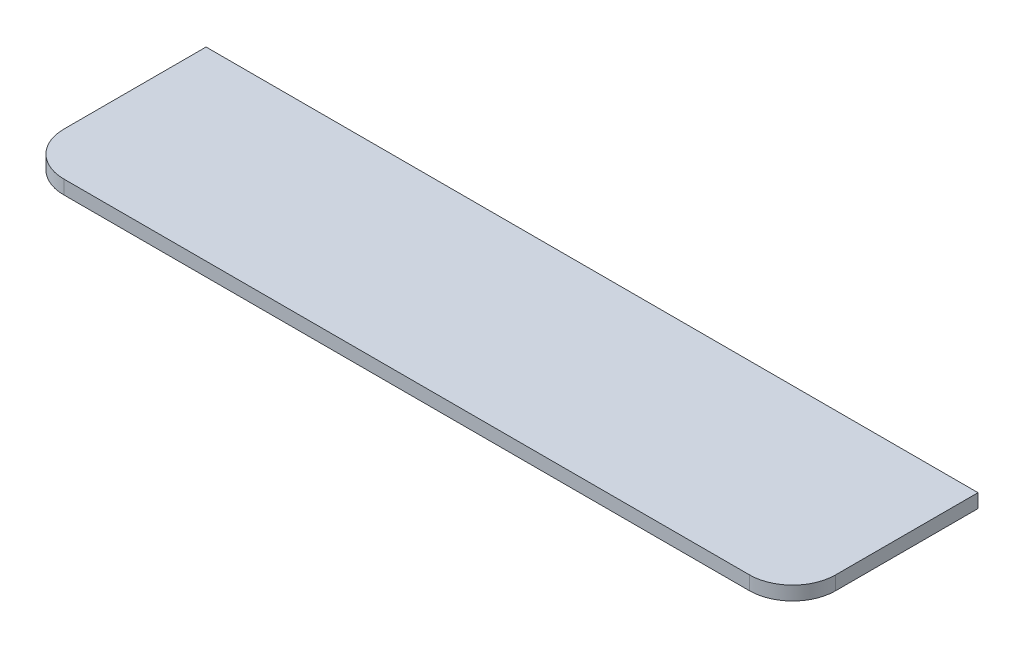
SolidWorks part; units mm, degrees
ref_plane "Спереди" through (0, 0, 0) normal (0, 0, 1) x (1, 0, 0)
ref_plane "Сверху" through (0, 0, 0) normal (0, 1, 0) x (1, 0, 0)
ref_plane "Справа" through (0, 0, 0) normal (1, 0, 0) x (0, 0, -1)
sketch "Эскиз1" plane through (0, 0, 0) normal (0, 1, 0) x (1, 0, 0)
  line L1 (0, 0) -> (895, 0)
  line L2 (0, 0) -> (0, -165)
  line L3 (50, -215) -> (845, -215)
  line L4 (895, 0) -> (895, -165)
  arc A0 (845, -215) -> (895, -165) centre (845, -165) ccw
  arc A1 (0, -165) -> (50, -215) centre (50, -165) ccw
  point P9 (0, -215)
  dimension "D3" = 50
  dimension "D1" = 895
  dimension "D2" = 215
extrude "Бобышка-Вытянуть1" add sketch "Эскиз1" along normal blind 16
